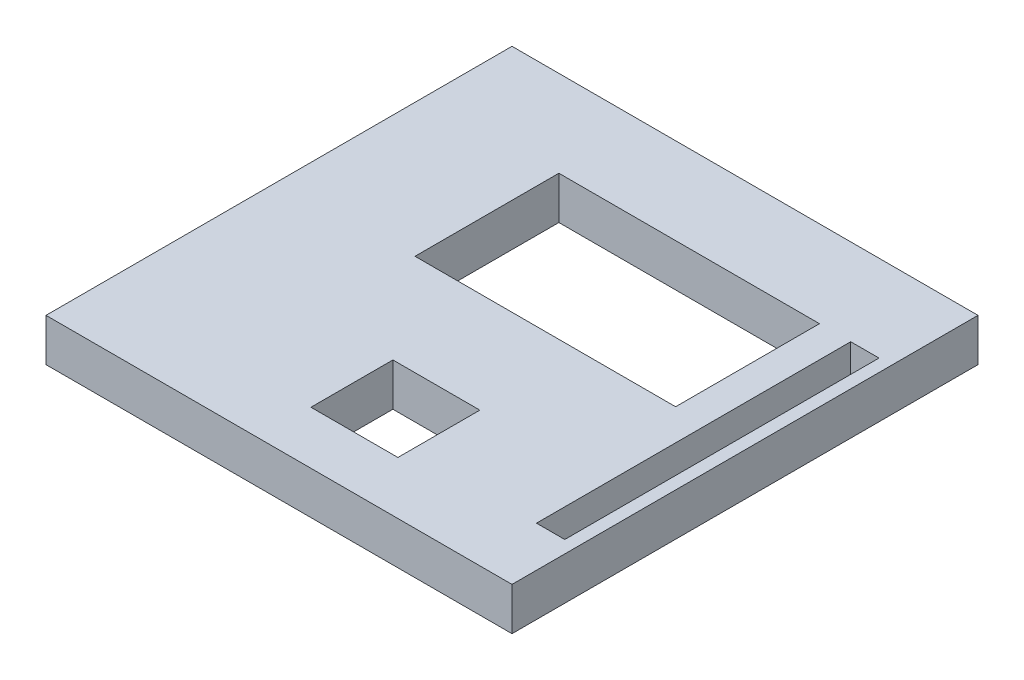
SolidWorks part; units mm, degrees
ref_plane "Front Plane" through (0, 0, 0) normal (0, 0, 1) x (1, 0, 0)
ref_plane "Top Plane" through (0, 0, 0) normal (0, 1, 0) x (1, 0, 0)
ref_plane "Right Plane" through (0, 0, 0) normal (1, 0, 0) x (0, 0, -1)
sketch "Sketch2" plane through (0, 0, 0) normal (0, 1, 0) x (1, 0, 0)
  line L1 (-54.6108, 53.5329) -> (65.3892, 53.5329)
  line L2 (-54.6108, 53.5329) -> (-54.6108, -66.4671)
  line L3 (-54.6108, -66.4671) -> (65.3892, -66.4671)
  line L4 (65.3892, 53.5329) -> (65.3892, -66.4671)
  dimension "D1" = 120
  dimension "D2" = 120
extrude "Boss-Extrude1" add sketch "Sketch2" along normal blind 11
sketch "Sketch3" plane through (0, 11, 0) normal (0, 1, 0) x (1, 0, 0)
  line L1 (-20.2697, 31.2622) -> (46.8383, 31.2622)
  line L2 (-20.2697, 31.2622) -> (-20.2697, -5.7838)
  line L3 (-20.2697, -5.7838) -> (46.8383, -5.7838)
  line L4 (46.8383, 31.2622) -> (46.8383, -5.7838)
  line L5 (0, -31.7465) -> (22.394, -31.7465)
  line L6 (0, -31.7465) -> (0, -52.8506)
  line L7 (0, -52.8506) -> (22.394, -52.8506)
  line L8 (22.394, -31.7465) -> (22.394, -52.8506)
  line L9 (54.8852, 31.2622) -> (62.173, 31.2622)
  line L10 (54.8852, 31.2622) -> (54.8852, -49.6622)
  line L11 (54.8852, -49.6622) -> (62.173, -49.6622)
  line L12 (62.173, 31.2622) -> (62.173, -49.6622)
extrude "Cut-Extrude1" cut sketch "Sketch3" against normal blind 33
